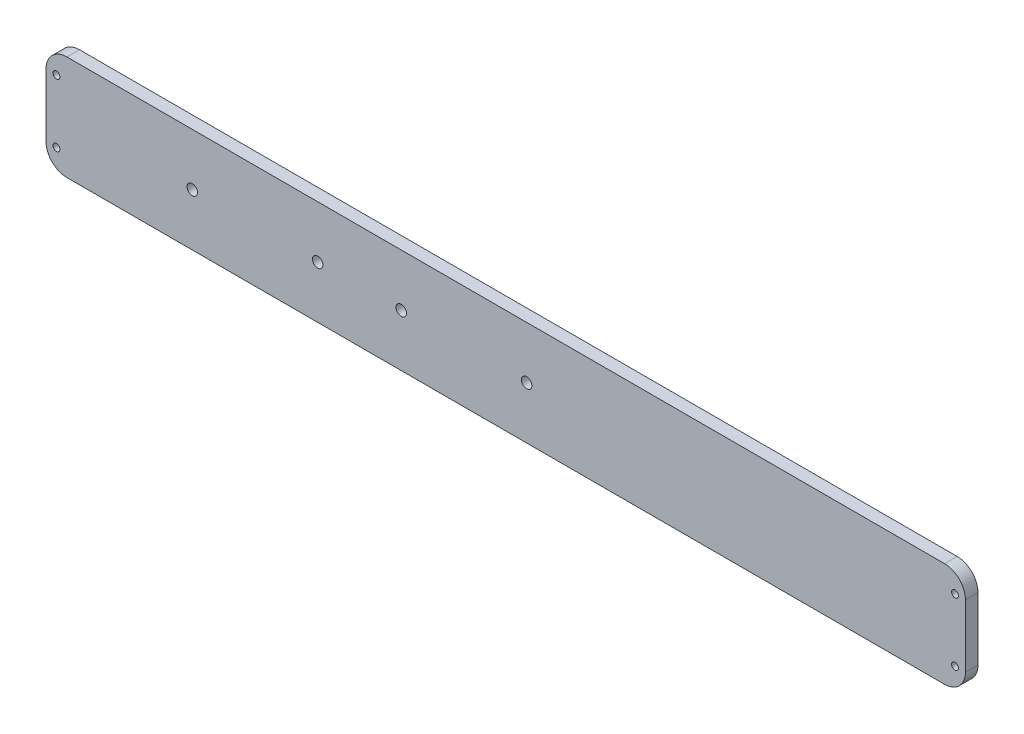
SolidWorks part; units mm, degrees
ref_plane "Plan de face" through (0, 0, 0) normal (0, 0, 1) x (1, 0, 0)
ref_plane "Plan de dessus" through (0, 0, 0) normal (0, 1, 0) x (1, 0, 0)
ref_plane "Plan de droite" through (0, 0, 0) normal (1, 0, 0) x (0, 0, -1)
sketch "Esquisse1" plane through (0, 0, 0) normal (0, 0, 1) x (1, 0, 0)
  line L1 (210, -25) -> (-210, -25)
  line L2 (220, -15) -> (220, 15)
  line L3 (210, 25) -> (-210, 25)
  line L4 (-220, -15) -> (-220, 15)
  line L5 (220, -25) -> (-220, 25) construction
  line L6 (220, 25) -> (-220, -25) construction
  arc A0 (220, 15) -> (210, 25) centre (210, 15) ccw
  arc A1 (210, -25) -> (220, -15) centre (210, -15) ccw
  arc A2 (-210, -25) -> (-220, -15) centre (-210, -15) cw
  arc A3 (-210, 25) -> (-220, 15) centre (-210, 15) ccw
  point P0 (0, 0)
  dimension "D3" = 10
  dimension "D1" = 440
  dimension "D2" = 50
extrude "Boss.-Extru.1" add sketch "Esquisse1" along normal blind 6
sketch "Esquisse2" plane through (0, 0, 6) normal (0, 0, 1) x (1, 0, 0)
  line L0 (-215, 15) -> (-215, -15) construction
  line L1 (215, 15) -> (215, -15) construction
  line L2 (-215, 0) -> (-220, 0) construction
  line L3 (-220, 15) -> (-220, -15) construction
  line L4 (215, 0) -> (220, 0) construction
  line L5 (220, -15) -> (220, 15) construction
  line L6 (-220, 0) -> (-150, 0) construction
  line L7 (-150, 0) -> (-90, 0) construction
  line L8 (-90, 0) -> (-50, 0) construction
  line L9 (-50, 0) -> (10, 0) construction
  circle A0 centre (215, 15) radius 1.65
  circle A1 centre (215, -15) radius 1.65
  circle A2 centre (-215, 15) radius 1.65
  circle A3 centre (-215, -15) radius 1.65
  circle A4 centre (-150, 0) radius 2.5
  circle A5 centre (-90, 0) radius 2.5
  circle A6 centre (-50, 0) radius 2.5
  circle A7 centre (10, 0) radius 2.5
  dimension "D5" = 3.3
  dimension "D10" = 5
  dimension "D1" = 5
  dimension "D2" = 30
  dimension "D3" = 30
  dimension "D4" = 5
  dimension "D6" = 70
  dimension "D7" = 60
  dimension "D8" = 170
  dimension "D9" = 60
extrude "Enlèv. mat.-Extru.1" cut sketch "Esquisse2" against normal blind 6
hole_wizard "Trou pour taraudage pour trou taraudé M6x1.01" positions "Esquisse3D1" profile "Esquisse3" hole size "M6x1.0" standard "Ansi Metric"
sketch3d "Esquisse3D1"
  line L0 (-150, 0, 0) -> (-150, 0, 6) construction
  line L1 (-90, 0, 0) -> (-90, 0, 6) construction
  line L2 (-50, 0, 0) -> (-50, 0, 6) construction
  line L3 (10, 0, 0) -> (10, 0, 6) construction
  point P0 (-150, 0, 6)
  point P4 (-90, 0, 6)
  point P8 (-50, 0, 6)
  point P12 (10, 0, 6)
sketch "Esquisse3" plane through (-150, 0, 6) normal (1, 0, 0) x (0, -1, 0)
  line L0 (0, 0) -> (0, 16.5022)
  line L1 (0, 16.5022) -> (2.5, 15)
  line L2 (2.5, 15) -> (2.5, 0)
  line L5 (2.5, 0) -> (0, 0)
  line L10 (0, 16.5022) -> (-2.5, 15) construction
  line L11 (0, -6.35) -> (0, 107.95) construction
  dimension "Diamètre du perçage" = 5
  dimension "Profondeur du perçage" = 15
  dimension "Angle de pointe" = 118
hole_wizard "Trou pour taraudage pour trou taraudé M4x0.71" positions "Esquisse3D2" profile "Esquisse4" hole size "M4x0.7" standard "Ansi Metric"
sketch3d "Esquisse3D2"
  line L0 (-215, 15, 0) -> (-215, 15, 6) construction
  line L1 (-215, -15, 0) -> (-215, -15, 6) construction
  line L2 (215, 15, 0) -> (215, 15, 6) construction
  line L3 (215, -15, 0) -> (215, -15, 6) construction
  point P0 (-215, 15, 6)
  point P4 (-215, -15, 6)
  point P8 (215, 15, 6)
  point P12 (215, -15, 6)
sketch "Esquisse4" plane through (-215, 15, 6) normal (1, 0, 0) x (0, -1, 0)
  line L0 (0, 0) -> (0, 15.9914)
  line L1 (0, 15.9914) -> (1.65, 15)
  line L2 (1.65, 15) -> (1.65, 0)
  line L5 (1.65, 0) -> (0, 0)
  line L10 (0, 15.9914) -> (-1.65, 15) construction
  line L11 (0, -6.35) -> (0, 107.95) construction
  dimension "Diamètre du perçage" = 3.3
  dimension "Profondeur du perçage" = 15
  dimension "Angle de pointe" = 118
